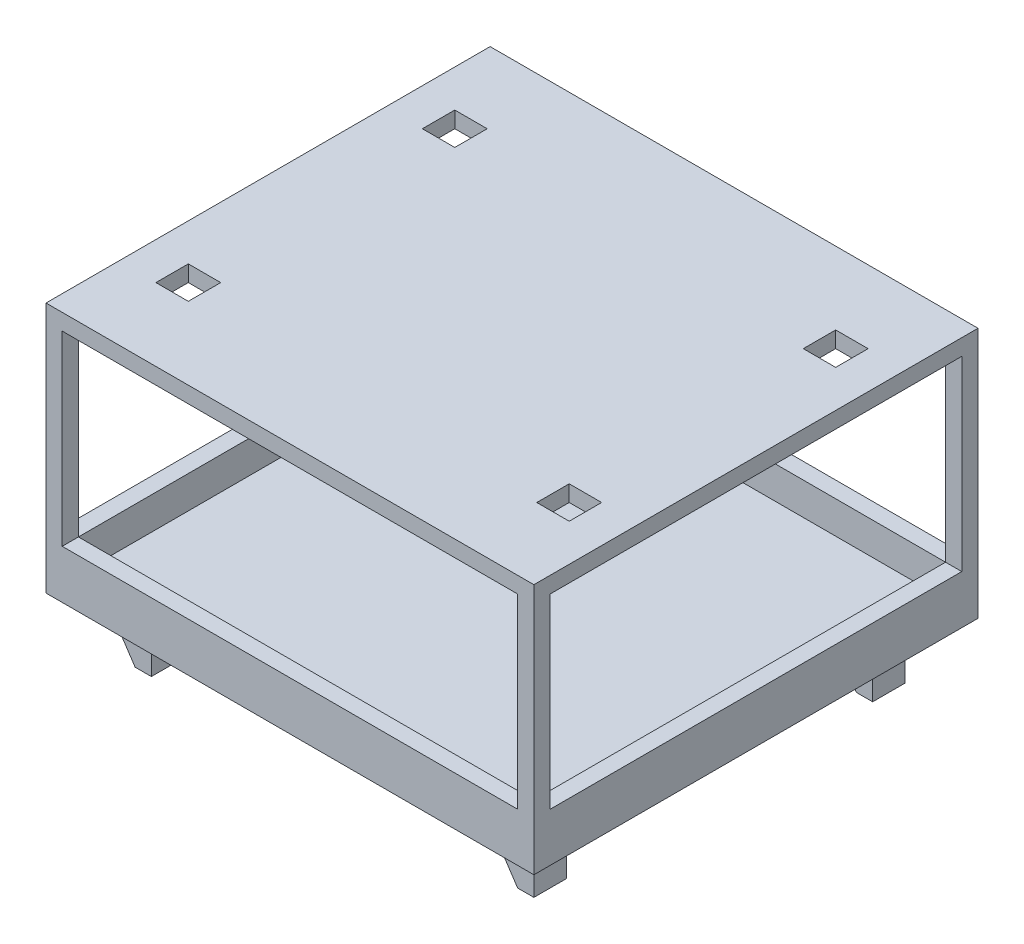
SolidWorks part; units mm, degrees
ref_plane "Front Plane" through (0, 0, 0) normal (0, 0, 1) x (1, 0, 0)
ref_plane "Top Plane" through (0, 0, 0) normal (0, 1, 0) x (1, 0, 0)
ref_plane "Right Plane" through (0, 0, 0) normal (1, 0, 0) x (0, 0, -1)
sketch "Sketch1" plane through (0, 0, 0) normal (0, 1, 0) x (1, 0, 0)
  line L0 (38.227, -34.798) -> (38.227, 34.798)
  line L1 (35.687, -32.258) -> (-35.687, -32.258) construction
  line L2 (35.687, -32.258) -> (35.687, 32.258) construction
  line L3 (35.687, 32.258) -> (-35.687, 32.258) construction
  line L4 (-35.687, -32.258) -> (-35.687, 32.258) construction
  line L5 (38.227, 34.798) -> (-38.227, 34.798)
  line L6 (-38.227, -34.798) -> (-38.227, 34.798)
  line L7 (38.227, -34.798) -> (-38.227, -34.798)
  point P0 (0, 0)
  point P6 (0, 32.258)
  point P7 (-35.687, 0)
  dimension "D1" = 71.374
  dimension "D2" = 64.516
  dimension "D3" = 2.54
extrude "Boss-Extrude1" add sketch "Sketch1" against normal blind 7.62
sketch "Sketch2" plane through (0, 0, 0) normal (0, 1, 0) x (1, 0, 0)
  line L0 (-35.687, -32.258) -> (35.687, -32.258)
  line L1 (35.687, -32.258) -> (35.687, 32.258)
  line L2 (35.687, 32.258) -> (-35.687, 32.258)
  line L3 (-35.687, 32.258) -> (-35.687, -32.258)
  line L4 (-38.227, -34.798) -> (38.227, -34.798)
  line L5 (38.227, -34.798) -> (38.227, 34.798)
  line L6 (38.227, 34.798) -> (-38.227, 34.798)
  line L7 (-38.227, 34.798) -> (-38.227, -34.798)
  line L8 (-38.227, -34.798) -> (38.227, -34.798) construction
  line L9 (38.227, -34.798) -> (38.227, 34.798) construction
  line L10 (38.227, 34.798) -> (-38.227, 34.798) construction
  line L11 (-38.227, 34.798) -> (-38.227, -34.798) construction
  dimension "D1" = 0
  dimension "D2" = 2.54
extrude "Cut-Extrude1" cut sketch "Sketch2" against normal blind 5.08
sketch "Sketch4" plane through (0, -7.62, 0) normal (0, -1, 0) x (1, 0, 0)
  line L0 (32.512, 29.083) -> (-32.512, 29.083) construction
  line L1 (-32.512, 29.083) -> (-32.512, -29.083) construction
  line L2 (-32.512, -29.083) -> (32.512, -29.083) construction
  line L3 (32.512, -29.083) -> (32.512, 29.083) construction
  line L4 (38.227, 34.798) -> (-38.227, 34.798)
  line L5 (-38.227, 34.798) -> (-38.227, -34.798)
  line L6 (-38.227, -34.798) -> (38.227, -34.798)
  line L7 (38.227, -34.798) -> (38.227, 34.798)
  line L8 (38.227, 34.798) -> (-38.227, 34.798) construction
  line L9 (-38.227, 34.798) -> (-38.227, -34.798) construction
  line L10 (-38.227, -34.798) -> (38.227, -34.798) construction
  line L11 (38.227, -34.798) -> (38.227, 34.798) construction
  line L12 (0, 0) -> (0, 29.083) construction
  line L13 (-32.512, 29.083) -> (-27.432, 29.083)
  line L14 (-32.512, 29.083) -> (-32.512, 24.003)
  line L15 (-32.512, 24.003) -> (-27.432, 24.003)
  line L16 (-27.432, 29.083) -> (-27.432, 24.003)
  line L17 (32.512, 24.003) -> (27.432, 24.003)
  line L18 (27.432, 29.083) -> (27.432, 24.003)
  line L19 (32.512, 29.083) -> (27.432, 29.083)
  line L20 (32.512, 29.083) -> (32.512, 24.003)
  dimension "D3" = 5.08
  dimension "D1" = 0
  dimension "D2" = 5.715
extrude "Boss-Extrude2" add sketch "Sketch4" along normal blind 8.7884
sketch "Sketch5" plane through (0, 0, 29.083) normal (0, 0, 1) x (1, 0, 0)
  line L1 (29.972, -16.4084) -> (27.432, -12.6069)
  line L3 (-27.432, -16.4084) -> (-32.512, -16.4084) construction
  line L4 (-29.972, -16.4084) -> (-32.512, -12.6069)
  line L5 (-32.512, -16.4084) -> (-32.512, -7.62) construction
  line L6 (27.432, -11.3369) -> (29.1531, -10.7982)
  line L7 (-32.512, -11.3369) -> (-30.7909, -10.7982)
  line L8 (-30.7909, -10.7982) -> (-30.7909, -7.62)
  line L9 (-38.227, -7.62) -> (38.227, -7.62) construction
  line L10 (-30.7909, -7.62) -> (-32.512, -7.62)
  line L11 (-32.512, -7.62) -> (-32.512, -11.3369)
  line L12 (-29.972, -16.4084) -> (-32.512, -16.4084)
  line L13 (-32.512, -16.4084) -> (-32.512, -12.6069)
  line L14 (29.1531, -7.62) -> (27.432, -7.62)
  line L15 (29.972, -16.4084) -> (27.432, -16.4084)
  line L16 (29.1531, -10.7982) -> (29.1531, -7.62)
  line L17 (27.432, -7.62) -> (27.432, -11.3369)
  line L18 (27.432, -16.4084) -> (27.432, -12.6069)
  dimension "D1" = 4.572
  dimension "D2" = 1.27
  dimension "D3" = 1.8034
  dimension "D4" = 4.572
  dimension "D5" = 1.27
  dimension "D6" = 1.8034
extrude "Cut-Extrude2" cut sketch "Sketch5" against normal up to next (5.08 mm away)
mirror "Mirror1" about plane through (0, 0, 0) normal (0, 0, 1) of "Cut-Extrude2", "Boss-Extrude2"
sketch "Sketch6" plane through (0, 0, 0) normal (0, 1, 0) x (1, 0, 0)
  line L0 (0, -29.9419) -> (0, 29.9419) construction
  line L1 (-38.227, 34.798) -> (-35.687, 34.798)
  line L2 (-38.227, 34.798) -> (-38.227, 32.258)
  line L3 (-38.227, 32.258) -> (-35.687, 32.258)
  line L4 (-35.687, 34.798) -> (-35.687, 32.258)
  line L5 (26.7876, 0) -> (-26.7876, 0) construction
  line L6 (-38.227, -32.258) -> (-35.687, -32.258)
  line L7 (-35.687, -34.798) -> (-35.687, -32.258)
  line L8 (-38.227, -34.798) -> (-35.687, -34.798)
  line L9 (-38.227, -34.798) -> (-38.227, -32.258)
  line L10 (38.227, -34.798) -> (38.227, -32.258)
  line L11 (38.227, -34.798) -> (35.687, -34.798)
  line L12 (35.687, -34.798) -> (35.687, -32.258)
  line L13 (38.227, -32.258) -> (35.687, -32.258)
  line L14 (38.227, 32.258) -> (35.687, 32.258)
  line L15 (35.687, 34.798) -> (35.687, 32.258)
  line L16 (38.227, 34.798) -> (35.687, 34.798)
  line L17 (38.227, 34.798) -> (38.227, 32.258)
  point P10 (0, 0)
  point P14 (0, 0)
extrude "Boss-Extrude3" add sketch "Sketch6" along normal blind 29.21
sketch "Sketch7" plane through (0, 29.21, 0) normal (0, 1, 0) x (1, 0, 0)
  line L1 (-38.227, -34.798) -> (38.227, -34.798)
  line L2 (-38.227, -34.798) -> (-38.227, 34.798)
  line L3 (-38.227, 34.798) -> (38.227, 34.798)
  line L4 (38.227, -34.798) -> (38.227, 34.798)
extrude "Boss-Extrude4" add sketch "Sketch7" along normal blind 2.54
sketch "Sketch8" plane through (0, 31.75, 0) normal (0, 1, 0) x (1, 0, 0)
  line L0 (0, -15.8687) -> (0, 15.8687) construction
  line L1 (21.0612, 0) -> (-21.0612, 0) construction
  line L2 (32.385, 18.3388) -> (27.305, 18.3388)
  line L3 (-32.385, 23.4188) -> (-27.305, 23.4188)
  line L4 (-38.227, 34.798) -> (-38.227, -34.798)
  line L5 (-38.227, -34.798) -> (38.227, -34.798)
  line L6 (38.227, -34.798) -> (38.227, 34.798)
  line L7 (38.227, 34.798) -> (-38.227, 34.798)
  line L8 (-38.227, 34.798) -> (-38.227, -34.798) construction
  line L9 (-38.227, -34.798) -> (38.227, -34.798) construction
  line L10 (38.227, -34.798) -> (38.227, 34.798) construction
  line L11 (38.227, 34.798) -> (-38.227, 34.798) construction
  line L12 (-32.385, 23.4188) -> (-32.385, 18.3388)
  line L13 (-32.385, 18.3388) -> (-27.305, 18.3388)
  line L14 (-27.305, 23.4188) -> (-27.305, 18.3388)
  line L15 (27.305, 23.4188) -> (27.305, 18.3388)
  line L16 (32.385, 23.4188) -> (27.305, 23.4188)
  line L17 (32.385, 23.4188) -> (32.385, 18.3388)
  line L18 (32.385, -23.4188) -> (32.385, -18.3388)
  line L19 (32.385, -23.4188) -> (27.305, -23.4188)
  line L20 (27.305, -23.4188) -> (27.305, -18.3388)
  line L21 (32.385, -18.3388) -> (27.305, -18.3388)
  line L22 (-32.385, -18.3388) -> (-27.305, -18.3388)
  line L23 (-27.305, -23.4188) -> (-27.305, -18.3388)
  line L24 (-32.385, -23.4188) -> (-27.305, -23.4188)
  line L25 (-32.385, -23.4188) -> (-32.385, -18.3388)
  point P7 (0, 0)
  point P12 (0, 0)
  dimension "D2" = 5.08
  dimension "D3" = 5.842
  dimension "D4" = 11.3792
  dimension "D1" = 0
extrude "Cut-Extrude3" cut sketch "Sketch8" against normal up to next
